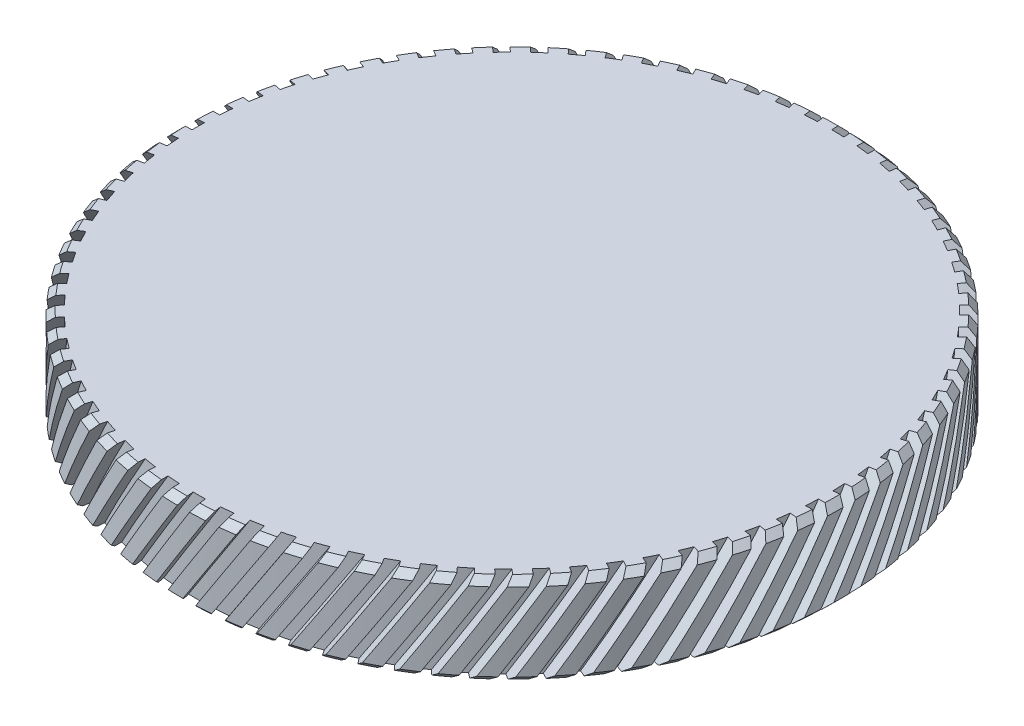
SolidWorks part; units mm, degrees
ref_plane "前视基准面" through (0, 0, 0) normal (0, 0, 1) x (1, 0, 0)
ref_plane "上视基准面" through (0, 0, 0) normal (0, 1, 0) x (1, 0, 0)
ref_plane "右视基准面" through (0, 0, 0) normal (1, 0, 0) x (0, 0, -1)
sketch "草图1" plane through (0, 0, 0) normal (0, 0, 1) x (1, 0, 0)
  line L0 (0, 46.0207) -> (0, -69.6142) construction
  line L1 (23.5, -8.8309) -> (24.1, -8.8309)
  line L2 (25.4, -6.3309) -> (0, -6.3309)
  line L3 (23.5, -13.3309) -> (25.4, -13.3309)
  line L4 (23.5, -13.3309) -> (23.5, -8.8309)
  line L5 (24.1, -8.8309) -> (24.1, -7.8309)
  line L6 (25.4, -13.3309) -> (25.4, -6.3309)
  line L7 (24.1, -7.8309) -> (0, -7.8309)
  line L8 (0, -7.8309) -> (0, -6.3309)
  dimension "D1" = 24.1
  dimension "D2" = 7
  dimension "D3" = 25.4
  dimension "D4" = 23.5
  dimension "D5" = 4.5
  dimension "D6" = 5.5
revolve "旋转1" add sketch "草图1" angle 360 about L0
cosmetic thread "装饰螺纹线1" parameters "D2"=48
chamfer "倒角1" distance 0.5 angle 45 2 edges at (0, -6.3309, 25.4) (0, -13.3309, 25.4)
surface "曲面-等距1" parameters "D1"=1
sketch "草图2" plane through (0, 0, 0) normal (0, 0, 1) x (1, 0, 0)
  line L0 (0, -2.7759) -> (-6.5923, -13.3309)
  line L1 (0, -2.7759) -> (0.6785, -3.1997)
  line L2 (-6.5923, -13.3309) -> (-5.9138, -13.7547)
  line L3 (0.6785, -3.1997) -> (-5.9138, -13.7547)
  line L4 (-24.9, -13.3309) -> (24.9, -13.3309) construction
extrude "切除-拉伸1" cut sketch "草图2" against normal up to surface (5.6 mm away) from offset 30
pattern_circular "阵列(圆周)1" count 75 over 360 about axis through (0, 0, 0) along (0, 1, 0) of "切除-拉伸1"
delete or keep bodies "实体-删除/保留 1" type delete bodies bodies 107
